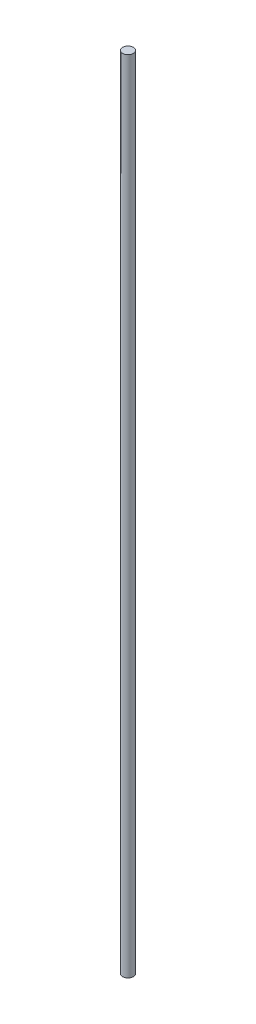
SolidWorks part; units mm, degrees
material "6061 Alloy"
ref_plane "Front Plane" through (0, 0, 0) normal (0, 0, 1) x (1, 0, 0)
ref_plane "Top Plane" through (0, 0, 0) normal (0, 1, 0) x (1, 0, 0)
ref_plane "Right Plane" through (0, 0, 0) normal (1, 0, 0) x (0, 0, -1)
sketch "Sketch1" plane through (0, 0, 0) normal (0, 1, 0) x (1, 0, 0)
  circle A0 centre (0, 0) radius 4
  dimension "D1" = 8
extrude "Boss-Extrude1" add sketch "Sketch1" along normal blind 600
